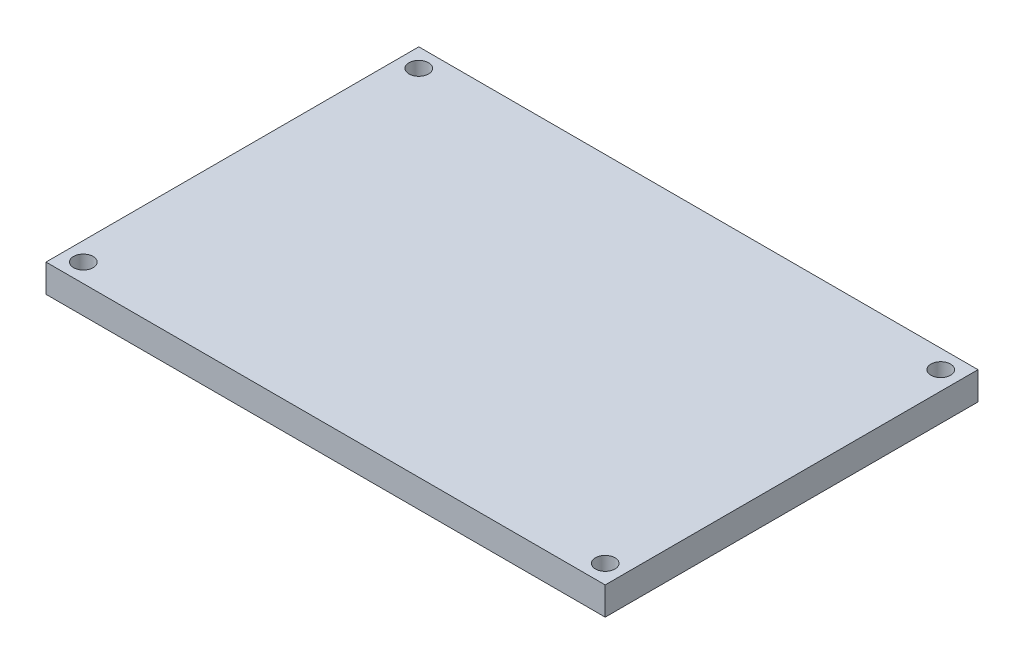
SolidWorks part; units mm, degrees
ref_plane "Alzado" through (0, 0, 0) normal (0, 0, 1) x (1, 0, 0)
ref_plane "Planta" through (0, 0, 0) normal (0, 1, 0) x (1, 0, 0)
ref_plane "Vista lateral" through (0, 0, 0) normal (1, 0, 0) x (0, 0, -1)
sketch "Croquis1" plane through (0, 0, 0) normal (0, 1, 0) x (1, 0, 0)
  line L0 (0, 0) -> (0, 20) construction
  line L1 (-30, 20) -> (30, 20)
  line L2 (-30, 20) -> (-30, -20)
  line L3 (-30, -20) -> (30, -20)
  line L4 (30, 20) -> (30, -20)
  circle A0 centre (-28, 18) radius 1.05
  circle A1 centre (-28, -18) radius 1.05
  circle A2 centre (28, -18) radius 1.05
  circle A3 centre (28, 18) radius 1.05
  point P11 (0, 0)
  point P18 (-27.5626, -20)
  dimension "D5" = 2.1
  dimension "D1" = 60
  dimension "D2" = 40
  dimension "D3" = 30
  dimension "D4" = 20
  dimension "D6" = 2
  dimension "D7" = 36
  dimension "D8" = 2
  dimension "D9" = 56
extrude "Saliente-Extruir1" add sketch "Croquis1" along normal blind 3
